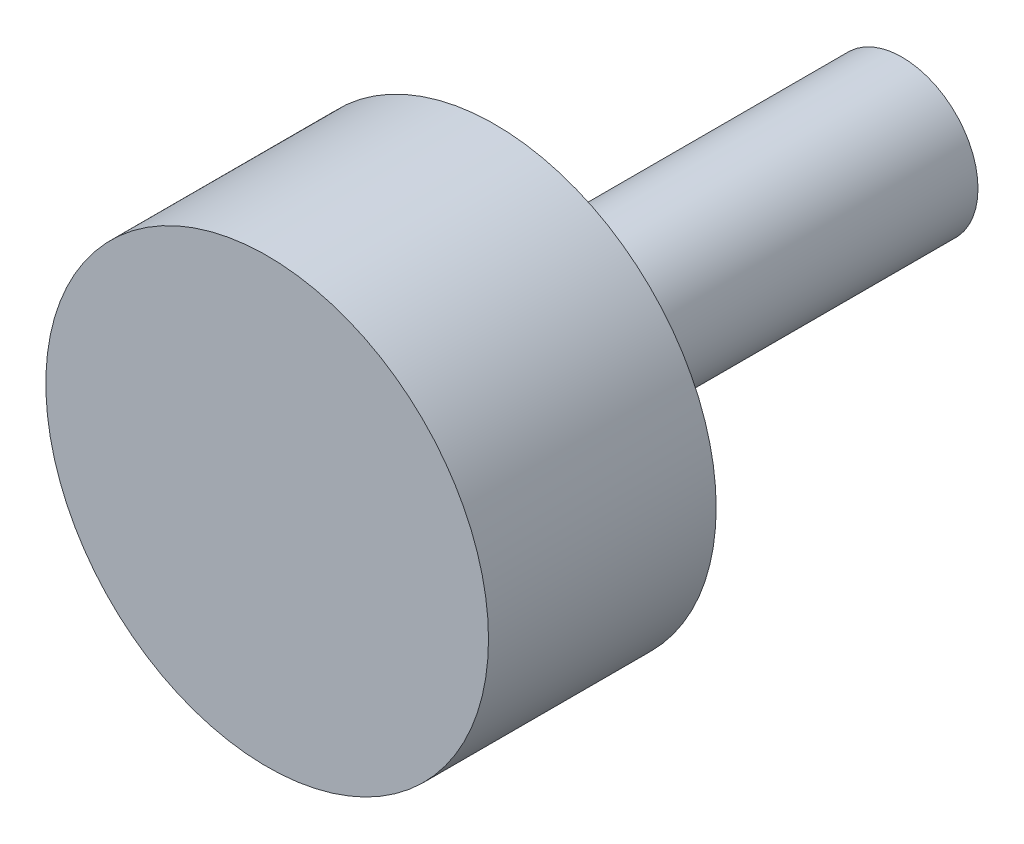
SolidWorks part; units mm, degrees
ref_plane "Front Plane" through (0, 0, 0) normal (0, 0, 1) x (1, 0, 0)
ref_plane "Top Plane" through (0, 0, 0) normal (0, 1, 0) x (1, 0, 0)
ref_plane "Right Plane" through (0, 0, 0) normal (1, 0, 0) x (0, 0, -1)
sketch "Sketch1" plane through (0, 0, 0) normal (0, 0, 1) x (1, 0, 0)
  circle A0 centre (0, 0) radius 6
  dimension "D1" = 12
extrude "Boss-Extrude1" add sketch "Sketch1" along normal blind 32.2
sketch "Sketch2" plane through (0, 0, 32.2) normal (0, 0, 1) x (1, 0, 0)
  circle A0 centre (0, 0) radius 17.5
  dimension "D1" = 35
extrude "Boss-Extrude2" add sketch "Sketch2" along normal blind 18
sketch "Sketch3" plane through (0, 0, 0) normal (0, 0, -1) x (-1, 0, 0)
  circle A0 centre (0, 0) radius 2.9
  dimension "D1" = 5.8
extrude "Cut-Extrude1" cut sketch "Sketch3" against normal blind 18
